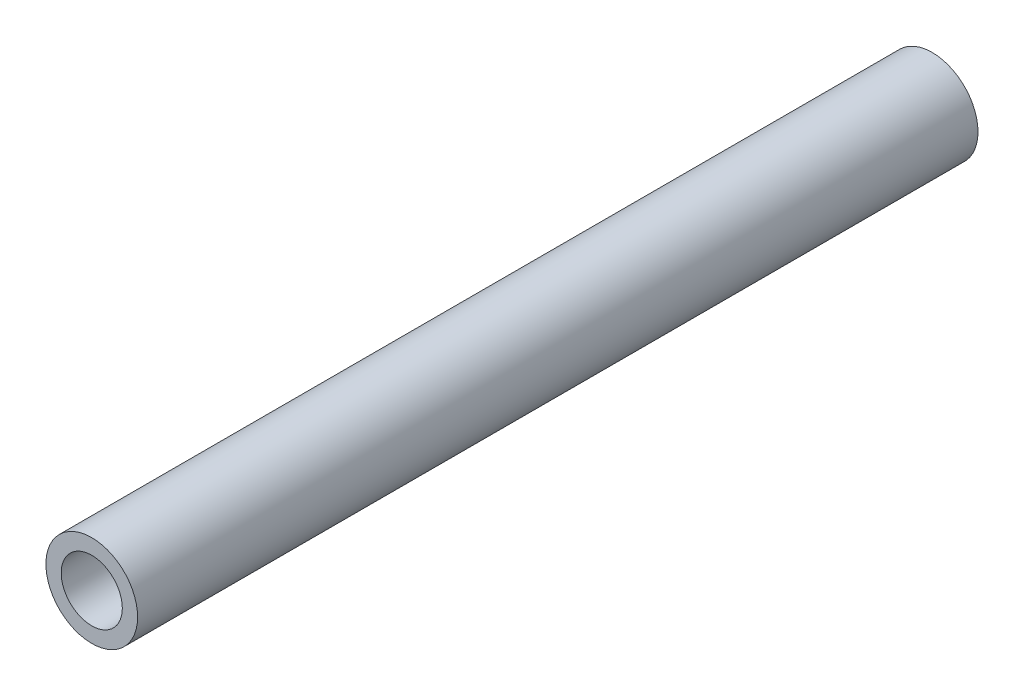
SolidWorks part; units mm, degrees
ref_plane "前视基准面" through (0, 0, 0) normal (0, 0, 1) x (1, 0, 0)
ref_plane "上视基准面" through (0, 0, 0) normal (0, 1, 0) x (1, 0, 0)
ref_plane "右视基准面" through (0, 0, 0) normal (1, 0, 0) x (0, 0, -1)
sketch "草图1" plane through (0, 0, 0) normal (0, 0, 1) x (1, 0, 0)
  circle A0 centre (0, 0) radius 3
  circle A1 centre (0, 0) radius 2
  dimension "D1" = 4
  dimension "D2" = 6
extrude "凸台-拉伸1" add sketch "草图1" along normal mid plane 55
